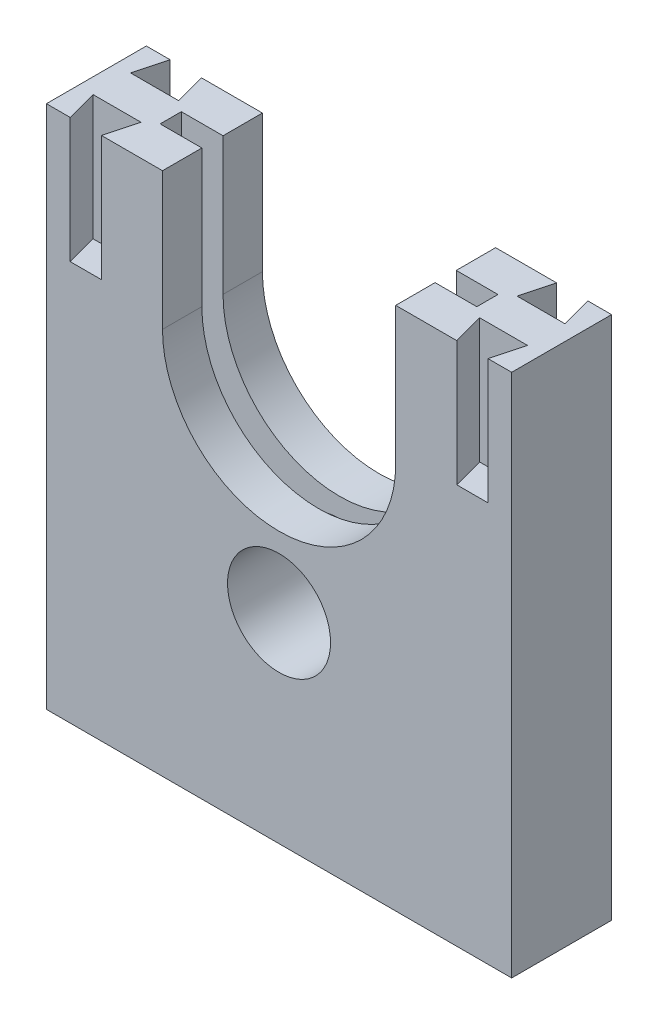
SolidWorks part; units mm, degrees
ref_plane "Front Plane" through (0, 0, 0) normal (0, 0, 1) x (1, 0, 0)
ref_plane "Top Plane" through (0, 0, 0) normal (0, 1, 0) x (1, 0, 0)
ref_plane "Right Plane" through (0, 0, 0) normal (1, 0, 0) x (0, 0, -1)
sketch "Sketch2" plane through (0, 0, 0) normal (0, 0, 1) x (1, 0, 0)
  line L1 (-19.4872, 32.4615) -> (16.5128, 32.4615)
  line L2 (-19.4872, 32.4615) -> (-19.4872, -9.5385)
  line L3 (-19.4872, -9.5385) -> (16.5128, -9.5385)
  line L4 (16.5128, 32.4615) -> (16.5128, -9.5385)
  dimension "D1" = 36
  dimension "D2" = 42
extrude "Boss-Extrude1" add sketch "Sketch2" along normal blind 8
sketch "Sketch3" plane through (0, 32.4615, 0) normal (0, 1, 0) x (1, 0, 0)
  line L0 (-19.4872, 0) -> (-18.2122, 0) construction
  line L1 (16.5128, 0) -> (-19.4872, 0) construction
  line L2 (-18.2122, 0) -> (-18.8821, -2.5)
  line L3 (-18.8821, -2.5) -> (-15.0423, -2.5)
  line L4 (-15.0423, -2.5) -> (-15.7122, 0)
  line L6 (-19.4872, -8) -> (-18.2122, -8) construction
  line L7 (16.5128, -8) -> (-19.4872, -8) construction
  line L8 (-18.2122, -8) -> (-18.8821, -5.5)
  line L9 (-18.8821, -5.5) -> (-15.0423, -5.5)
  line L10 (-15.0423, -5.5) -> (-15.7122, -8)
  line L12 (16.5128, 0) -> (15.2378, 0) construction
  line L13 (15.2378, 0) -> (15.9077, -2.5)
  line L14 (15.9077, -2.5) -> (12.0679, -2.5)
  line L15 (12.0679, -2.5) -> (12.7378, 0)
  line L16 (16.5128, -8) -> (15.2378, -8) construction
  line L17 (15.2378, -8) -> (15.9077, -5.5)
  line L18 (15.9077, -5.5) -> (12.0679, -5.5)
  line L19 (12.0679, -5.5) -> (12.7378, -8)
  line L20 (-15.7122, 0) -> (-18.2122, 0)
  line L21 (-18.2122, -8) -> (-15.7122, -8)
  line L22 (15.2378, 0) -> (12.7378, 0)
  line L23 (15.2378, -8) -> (12.7378, -8)
  dimension "D1" = 1.275
  dimension "D2" = 2.5
  dimension "D3" = 2.5
  dimension "D4" = 2.5
  dimension "D5" = 105
  dimension "D6" = 105
  dimension "D7" = 1.275
  dimension "D8" = 2.5
  dimension "D9" = 105
  dimension "D10" = 105
  dimension "D11" = 2.5
  dimension "D12" = 1.275
  dimension "D13" = 2.5
  dimension "D14" = 2.5
  dimension "D15" = 105
  dimension "D16" = 105
  dimension "D17" = 1.275
  dimension "D18" = 2.5
  dimension "D19" = 2.5
  dimension "D20" = 105
  dimension "D21" = 105
ref_plane "Plane1" through (0, 0, 4) normal (0, 0, 1) x (1, 0, 0)
extrude "Cut-Extrude1" cut sketch "Sketch3" against normal blind 10
sketch "Sketch4" plane through (0, 0, 8) normal (0, 0, 1) x (1, 0, 0)
  line L0 (-15.7122, 32.4615) -> (12.7378, 32.4615) construction
  line L1 (-10.8235, 32.4615) -> (7.8491, 32.4615)
  line L2 (-19.4872, -9.5385) -> (16.5128, -9.5385) construction
  line L5 (7.8491, 21.4615) -> (7.8491, 32.4615)
  line L6 (-1.4872, -9.5385) -> (-1.4872, 32.4615) construction
  line L7 (-10.8235, 21.4615) -> (-10.8235, 32.4615)
  arc A1 (-10.8235, 21.4615) -> (7.8491, 21.4615) centre (-1.4872, 21.4615) ccw
  dimension "D1" = 11
extrude "Cut-Extrude2" cut sketch "Sketch4" against normal blind 10
sketch "Sketch5" plane through (0, 32.4615, 0) normal (0, 1, 0) x (1, 0, 0)
  line L0 (-19.4872, -8) -> (-19.4872, 0) construction
  line L5 (-19.4872, -4) -> (16.5128, -4) construction
  line L6 (16.5128, -8) -> (16.5128, 0) construction
  line L7 (-19.4872, 0) -> (16.5128, -8) construction
  line L9 (-14.1642, -4.8477) -> (11.1898, -4.8477)
  line L10 (-14.1642, -4.8477) -> (-14.1642, -3.1523)
  line L11 (-14.1642, -3.1523) -> (11.1898, -3.1523)
  line L12 (11.1898, -4.8477) -> (11.1898, -3.1523)
  line L13 (-14.1642, -4.8477) -> (11.1898, -3.1523) construction
  line L14 (-14.1642, -3.1523) -> (11.1898, -4.8477) construction
  point P0 (-1.4872, -4)
extrude "Cut-Extrude3" cut sketch "Sketch5" against normal blind 25
sketch "Sketch6" plane through (0, 0, 8) normal (0, 0, 1) x (1, 0, 0)
  circle A0 centre (-1.4919, 6.4615) radius 4.125
  dimension "D1" = 8.25
extrude "Cut-Extrude4" cut sketch "Sketch6" against normal blind 7.1
sketch "Sketch7" plane through (0, 32.4615, 0) normal (0, 1, 0) x (1, 0, 0)
  line L0 (16.5128, -8) -> (16.5128, 0) construction
  line L1 (-19.4872, 0) -> (-20.1172, 0)
  line L2 (-19.4872, 0) -> (-19.4872, -8)
  line L3 (-19.4872, -8) -> (-20.1172, -8)
  line L4 (-20.1172, 0) -> (-20.1172, -8)
  line L5 (16.5128, 0) -> (17.1331, 0)
  line L6 (16.5128, 0) -> (16.5128, -8)
  line L7 (16.5128, -8) -> (17.1331, -8)
  line L8 (17.1331, 0) -> (17.1331, -8)
  dimension "D1" = 8
  dimension "D2" = 0.63
extrude "Boss-Extrude2" add sketch "Sketch7" against normal blind 42
